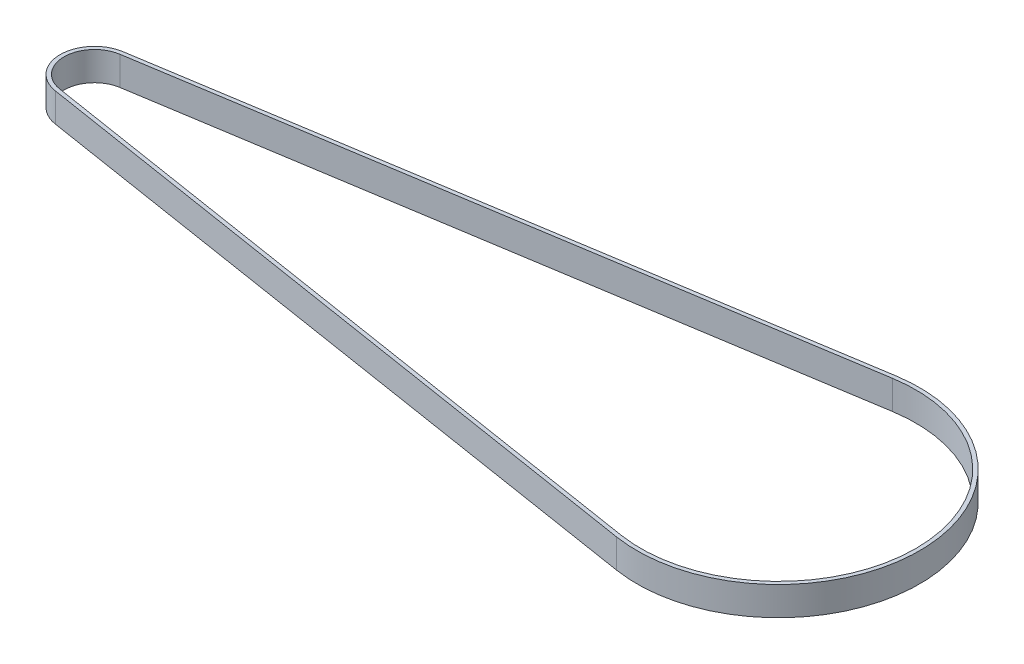
SolidWorks part; units mm, degrees
ref_plane "Front Plane" through (0, 0, 0) normal (0, 0, 1) x (1, 0, 0)
ref_plane "Top Plane" through (0, 0, 0) normal (0, 1, 0) x (1, 0, 0)
ref_plane "Right Plane" through (0, 0, 0) normal (1, 0, 0) x (0, 0, -1)
sketch "Sketch1" plane through (0, 0, 0) normal (0, 1, 0) x (1, 0, 0)
  line L0 (-143.4937, 6.2718) -> (-4.4835, 28.297)
  line L1 (-143.4937, -6.2718) -> (-4.4835, -28.297)
  line L2 (-143.6189, 7.0619) -> (-4.6087, 29.0872)
  line L3 (-143.6189, -7.0619) -> (-4.6087, -29.0872)
  arc A0 (-4.4835, -28.297) -> (-4.4835, 28.297) centre (0, 0) ccw
  arc A1 (-143.4937, 6.2718) -> (-143.4937, -6.2718) centre (-142.5, 0) ccw
  arc A2 (-4.6087, -29.0872) -> (-4.6087, 29.0872) centre (0, 0) ccw
  arc A3 (-143.6189, 7.0619) -> (-143.6189, -7.0619) centre (-142.5, 0) ccw
  dimension "D1" = 12.7
  dimension "D2" = 57.3
  dimension "D3" = 142.5
  dimension "D4" = 0.8
extrude "Boss-Extrude1" add sketch "Sketch1" along normal blind 6
